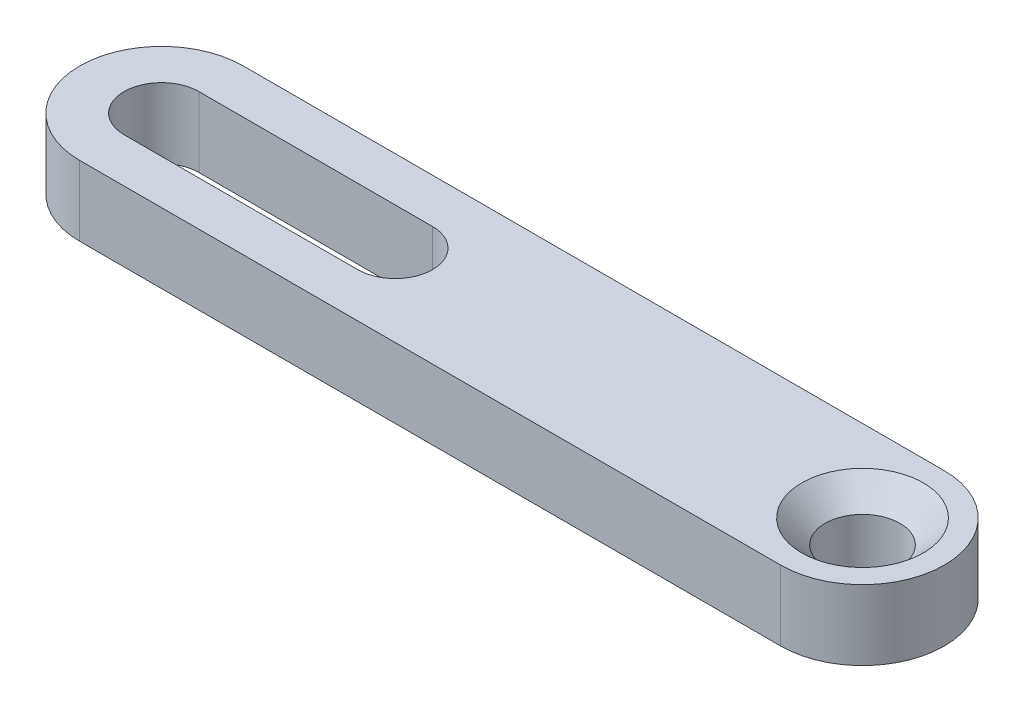
SolidWorks part; units mm, degrees
ref_plane "Спереди" through (0, 0, 0) normal (0, 0, 1) x (1, 0, 0)
ref_plane "Сверху" through (0, 0, 0) normal (0, 1, 0) x (1, 0, 0)
ref_plane "Справа" through (0, 0, 0) normal (1, 0, 0) x (0, 0, -1)
sketch "Эскиз1" plane through (0, 0, 0) normal (0, 1, 0) x (1, 0, 0)
  line L0 (-30, 1.6) -> (-20, 1.6)
  line L1 (-30, -1.6) -> (-20, -1.6)
  line L2 (-30, 3.5) -> (0, 3.5)
  line L3 (-30, -3.5) -> (0, -3.5)
  circle A0 centre (0, 0) radius 1.6
  arc A1 (0, -3.5) -> (0, 3.5) centre (0, 0) ccw
  arc A2 (-20, -1.6) -> (-20, 1.6) centre (-20, 0) ccw
  arc A3 (-30, 1.6) -> (-30, -1.6) centre (-30, 0) ccw
  arc A4 (-30, 3.5) -> (-30, -3.5) centre (-30, 0) ccw
  dimension "D1" = 3.2
  dimension "D2" = 7
  dimension "D3" = 3.2
  dimension "D5" = 3.2
  dimension "D7" = 7
  dimension "D4" = 20
  dimension "D6" = 30
extrude "Бобышка-Вытянуть1" add sketch "Эскиз1" along normal blind 3
chamfer "Фаска1" distance 1 angle 45 1 edges at (0, 3, 1.6)
